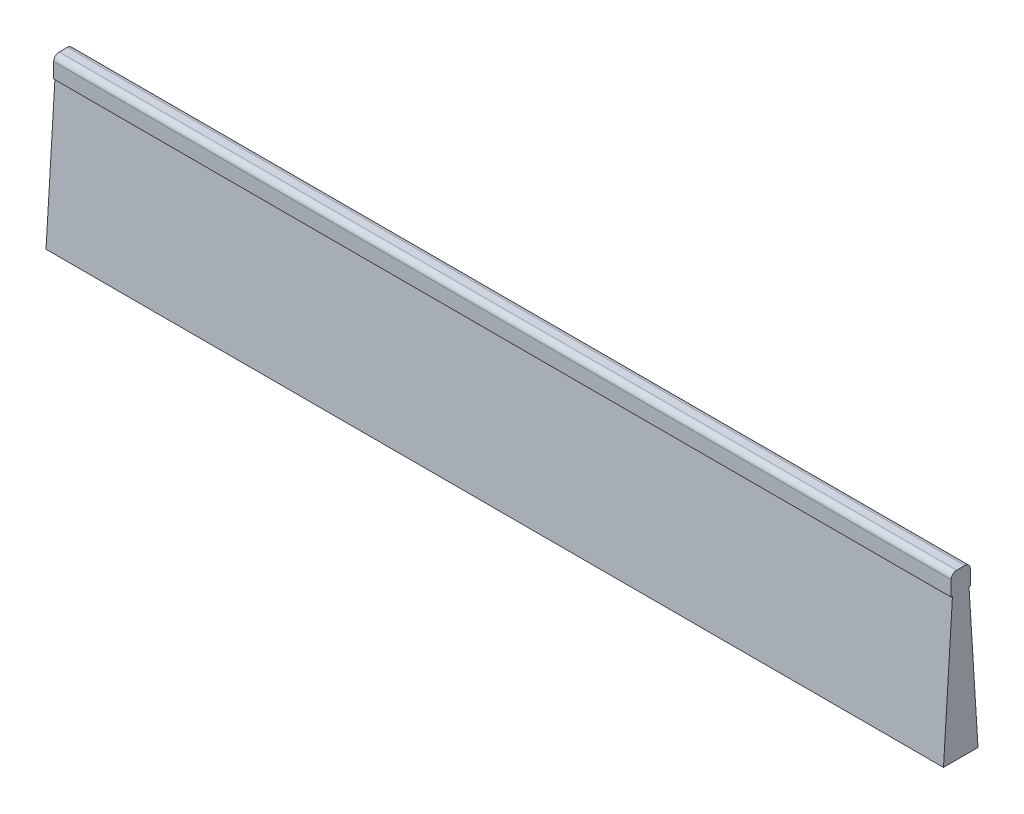
SolidWorks part; units mm, degrees
material "PA Type 6"
ref_plane "Front Plane" through (0, 0, 0) normal (0, 0, 1) x (1, 0, 0)
ref_plane "Top Plane" through (0, 0, 0) normal (0, 1, 0) x (1, 0, 0)
ref_plane "Right Plane" through (0, 0, 0) normal (1, 0, 0) x (0, 0, -1)
sketch "Sketch1" plane through (0, 0, 0) normal (1, 0, 0) x (0, 0, -1)
  line L0 (-1.3208, 0) -> (1.3208, 0)
  line L1 (2.6194, 0) -> (-2.6194, 0) construction
  line L2 (1.3208, 0) -> (1.3208, -2.8448)
  line L3 (1.3208, -2.8448) -> (1.143, -2.8448)
  line L4 (1.143, -2.8448) -> (2.3813, -22.6568)
  line L5 (2.3813, -22.6568) -> (-2.3812, -22.6568)
  line L6 (0, 12.7406) -> (0, -12.7406) construction
  line L7 (0, 23.9962) -> (0, -77.5742) construction
  line L8 (-1.143, -2.8448) -> (-2.3812, -22.6568)
  line L9 (-1.3208, -2.8448) -> (-1.143, -2.8448)
  line L10 (-1.3208, 0) -> (-1.3208, -2.8448)
  point P14 (0, -22.6568)
  point P17 (0, 0)
  dimension "D1" = 2.8448
  dimension "D2" = 2.6416
  dimension "D3" = 19.812
  dimension "D4" = 4.7625
  dimension "D5" = 2.286
extrude "Boss-Extrude1" add sketch "Sketch1" along normal mid plane 123.825
fillet "Fillet1" radius 0.762 2 edges at (0, 0, 1.3208) (0, 0, -1.3208)
